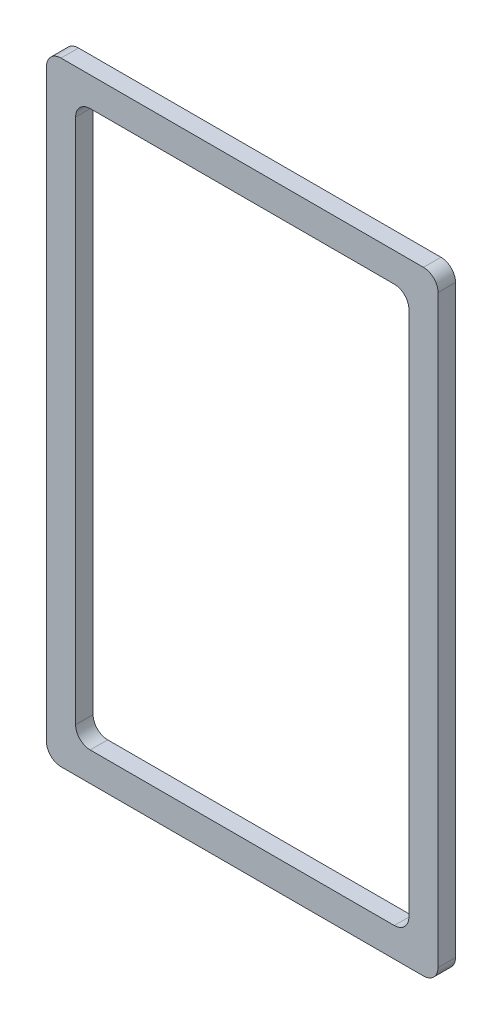
SolidWorks part; units mm, degrees
material "有机玻璃 (TM) GS 丙烯酸铸钣"
ref_plane "前视基准面" through (0, 0, 0) normal (0, 0, 1) x (1, 0, 0)
ref_plane "上视基准面" through (0, 0, 0) normal (0, 1, 0) x (1, 0, 0)
ref_plane "右视基准面" through (0, 0, 0) normal (1, 0, 0) x (0, 0, -1)
sketch "草图1" plane through (0, 0, 0) normal (0, 0, 1) x (1, 0, 0)
  line L1 (2.5, 0) -> (64.6502, 0)
  line L2 (0, 2.5) -> (0, 102.7498)
  line L3 (2.5, 105.2498) -> (64.6502, 105.2498)
  line L4 (67.1502, 2.5) -> (67.1502, 102.7498)
  line L5 (7.5, 100.2498) -> (59.6502, 100.2498)
  line L6 (5, 97.7498) -> (5, 7.5)
  line L7 (7.5, 5) -> (59.6502, 5)
  line L8 (62.1502, 97.7498) -> (62.1502, 7.5)
  arc A0 (0, 2.5) -> (2.5, 0) centre (2.5, 2.5) ccw
  arc A1 (67.1502, 102.7498) -> (64.6502, 105.2498) centre (64.6502, 102.7498) ccw
  arc A2 (2.5, 105.2498) -> (0, 102.7498) centre (2.5, 102.7498) ccw
  arc A3 (64.6502, 0) -> (67.1502, 2.5) centre (64.6502, 2.5) ccw
  arc A4 (59.6502, 5) -> (62.1502, 7.5) centre (59.6502, 7.5) ccw
  arc A5 (7.5, 5) -> (5, 7.5) centre (7.5, 7.5) cw
  arc A6 (62.1502, 97.7498) -> (59.6502, 100.2498) centre (59.6502, 97.7498) ccw
  arc A7 (7.5, 100.2498) -> (5, 97.7498) centre (7.5, 97.7498) ccw
  point P9 (0, 0)
  point P18 (0, 0)
  point P19 (0, 0)
  point P20 (63.7247, 5.209)
  point P21 (0, 0)
  point P22 (0, 0)
  point P23 (0, 0)
  point P24 (0, 0)
  point P25 (0, 0)
  point P26 (0, 0)
  dimension "D1" = 2.5
  dimension "D2" = 2.5
extrude "凸台-拉伸1" add sketch "草图1" along normal blind 3
